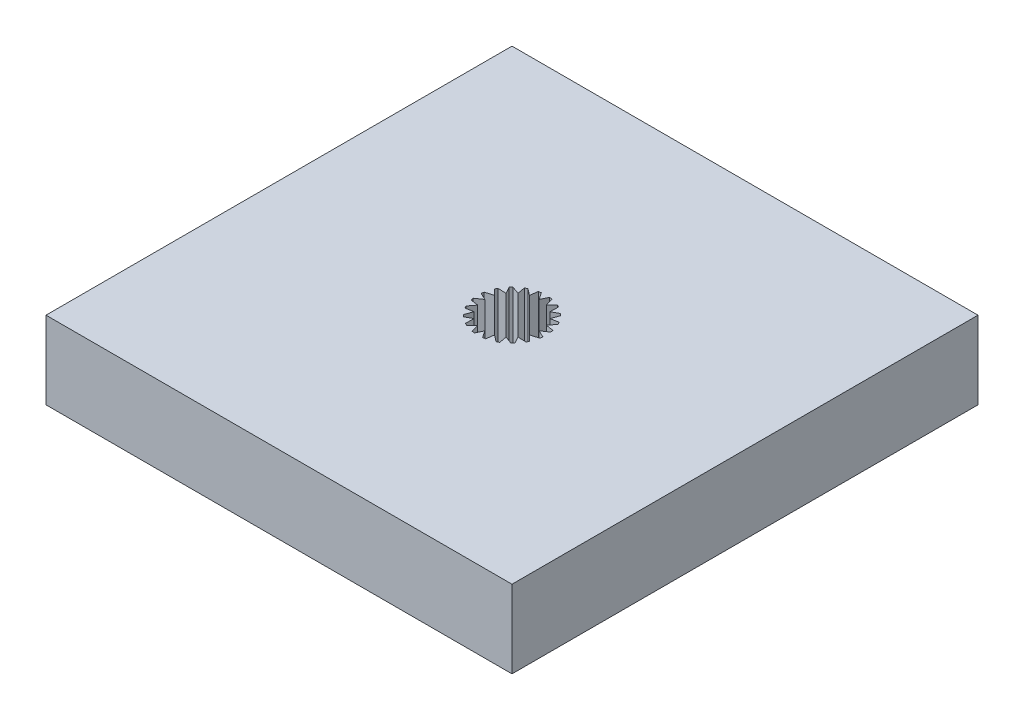
SolidWorks part; units mm, degrees
ref_plane "Front Plane" through (0, 0, 0) normal (0, 0, 1) x (1, 0, 0)
ref_plane "Top Plane" through (0, 0, 0) normal (0, 1, 0) x (1, 0, 0)
ref_plane "Right Plane" through (0, 0, 0) normal (1, 0, 0) x (0, 0, -1)
sketch "Sketch4" plane through (0, 0, 0) normal (0, 1, 0) x (1, 0, 0)
  line L0 (-1.9497, 2.0278) -> (-1.3068, 1.7987)
  line L1 (-1.3068, 1.7987) -> (-1.4208, 2.4279)
  line L2 (-1.4208, 2.4279) -> (-1.2276, 2.531)
  line L3 (-1.2276, 2.531) -> (-0.687, 2.1145)
  line L4 (-0.687, 2.1145) -> (-0.601, 2.7481)
  line L5 (-0.601, 2.7481) -> (-0.3854, 2.7865)
  line L6 (-0.3854, 2.7865) -> (0, 2.2233)
  line L7 (0, 2.2233) -> (0.2777, 2.7993)
  line L8 (0.2777, 2.7993) -> (0.4945, 2.7692)
  line L9 (0.4945, 2.7692) -> (0.687, 2.1145)
  line L10 (0.687, 2.1145) -> (1.1291, 2.5765)
  line L11 (1.1291, 2.5765) -> (1.3261, 2.4809)
  line L12 (1.3261, 2.4809) -> (1.3068, 1.7987)
  line L13 (1.3068, 1.7987) -> (1.87, 2.1015)
  line L14 (1.87, 2.1015) -> (2.0278, 1.9497)
  line L15 (2.0278, 1.9497) -> (1.7987, 1.3068)
  line L16 (1.7987, 1.3068) -> (2.4279, 1.4208)
  line L17 (2.4279, 1.4208) -> (2.531, 1.2276)
  line L18 (2.531, 1.2276) -> (2.1145, 0.687)
  line L19 (2.1145, 0.687) -> (2.7481, 0.601)
  line L20 (2.7481, 0.601) -> (2.7865, 0.3854)
  line L21 (2.7865, 0.3854) -> (2.2233, 0)
  line L22 (2.2233, 0) -> (2.7993, -0.2777)
  line L23 (2.7993, -0.2777) -> (2.7692, -0.4945)
  line L24 (2.7692, -0.4945) -> (2.1145, -0.687)
  line L25 (2.1145, -0.687) -> (2.5765, -1.1291)
  line L26 (2.5765, -1.1291) -> (2.4809, -1.3261)
  line L27 (2.4809, -1.3261) -> (1.7987, -1.3068)
  line L28 (1.7987, -1.3068) -> (2.1015, -1.87)
  line L29 (2.1015, -1.87) -> (1.9497, -2.0278)
  line L30 (1.9497, -2.0278) -> (1.3164, -1.8021)
  line L31 (1.3164, -1.8021) -> (1.4208, -2.4279)
  line L32 (1.4208, -2.4279) -> (1.2276, -2.531)
  line L33 (1.2276, -2.531) -> (0.687, -2.1145)
  line L34 (0.687, -2.1145) -> (0.601, -2.7481)
  line L35 (0.601, -2.7481) -> (0.3854, -2.7865)
  line L36 (0.3854, -2.7865) -> (0, -2.2233)
  line L37 (0, -2.2233) -> (-0.2777, -2.7993)
  line L38 (-0.2777, -2.7993) -> (-0.4945, -2.7692)
  line L39 (-0.4945, -2.7692) -> (-0.687, -2.1145)
  line L40 (-0.687, -2.1145) -> (-1.1291, -2.5765)
  line L41 (-1.1291, -2.5765) -> (-1.3261, -2.4809)
  line L42 (-1.3261, -2.4809) -> (-1.3068, -1.7987)
  line L43 (-1.3068, -1.7987) -> (-1.87, -2.1015)
  line L44 (-1.87, -2.1015) -> (-2.0278, -1.9497)
  line L45 (-2.0278, -1.9497) -> (-1.7987, -1.3068)
  line L46 (-1.7987, -1.3068) -> (-2.4279, -1.4208)
  line L47 (-2.4279, -1.4208) -> (-2.531, -1.2276)
  line L48 (-2.531, -1.2276) -> (-2.1145, -0.687)
  line L49 (-2.1145, -0.687) -> (-2.7481, -0.601)
  line L50 (-2.7481, -0.601) -> (-2.7865, -0.3854)
  line L51 (-2.7865, -0.3854) -> (-2.2233, 0)
  line L52 (-2.2233, 0) -> (-2.7993, 0.2777)
  line L53 (-2.7993, 0.2777) -> (-2.7692, 0.4945)
  line L54 (-2.7692, 0.4945) -> (-2.1145, 0.687)
  line L55 (-2.1145, 0.687) -> (-2.5765, 1.1291)
  line L56 (-2.5765, 1.1291) -> (-2.4809, 1.3261)
  line L57 (-2.4809, 1.3261) -> (-1.7987, 1.3068)
  line L58 (-1.7987, 1.3068) -> (-2.1015, 1.87)
  line L59 (-2.1015, 1.87) -> (-1.9497, 2.0278)
  line L60 (-1.3068, 1.7987) -> (-1.9497, 2.0278)
  line L62 (-19.05, -19.05) -> (19.05, -19.05)
  line L63 (-19.05, -19.05) -> (-19.05, 19.05)
  line L64 (-19.05, 19.05) -> (19.05, 19.05)
  line L65 (19.05, -19.05) -> (19.05, 19.05)
  line L66 (-19.05, -19.05) -> (19.05, 19.05) construction
  line L67 (-19.05, 19.05) -> (19.05, -19.05) construction
  circle A1 centre (0, 0) radius 2.2233
  dimension "D1" = 38.1
  dimension "D2" = 4.4466
  dimension "D3" = 38.1
extrude "Boss-Extrude2" add sketch "Sketch4" along normal blind 6.35 contours L62 L65 L64 L63 L58 L59 L0 L1 L2 L3 L4 L5 L6 L7 L8 L9 L10 L11 L12 L13 L14 L15 L16 L17 L18 L19 L20 L21 L22 L23 L24 L25 L26 L27 L28 L29 L30 L31 L32 L33 L34 L35 L36 L37 L38 L39 L40 L41 L42 L43
